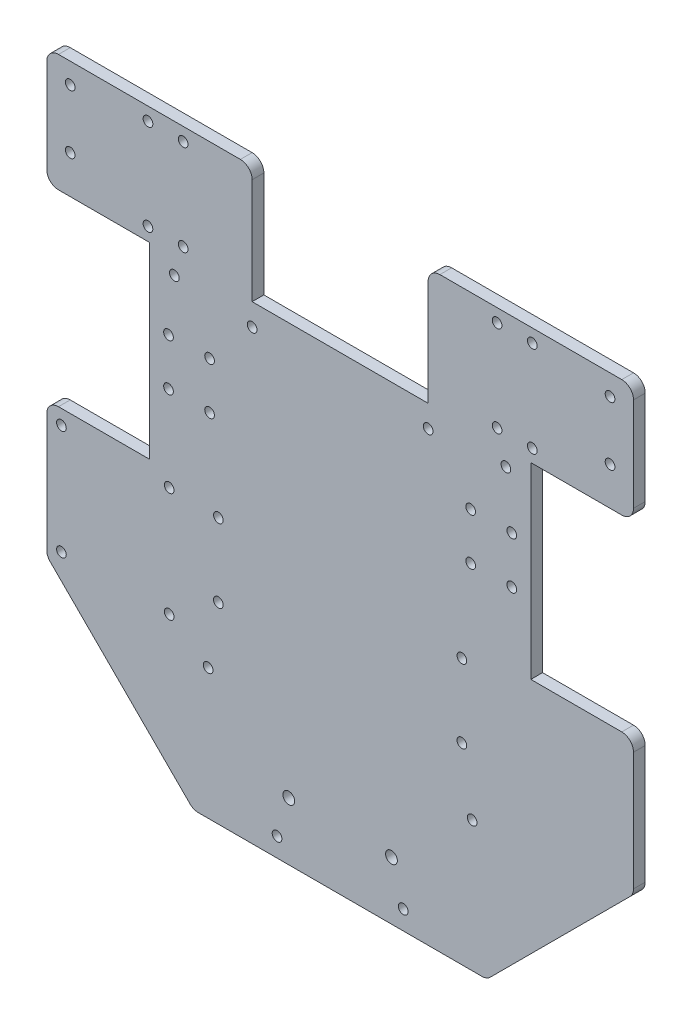
SolidWorks part; units mm, degrees
ref_plane "前视基准面" through (0, 0, 0) normal (0, 0, 1) x (1, 0, 0)
ref_plane "上视基准面" through (0, 0, 0) normal (0, 1, 0) x (1, 0, 0)
ref_plane "右视基准面" through (0, 0, 0) normal (1, 0, 0) x (0, 0, -1)
sketch "草图1" plane through (0, 0, 0) normal (0, 0, 1) x (1, 0, 0)
  line L0 (0, 0) -> (0, 207.9951) construction
  line L1 (-96, 200) -> (-30, 200)
  line L2 (-100, 196) -> (-100, 160)
  line L3 (-50, 0) -> (50, 0)
  line L4 (100, 196) -> (100, 160)
  line L5 (-100, 200) -> (74.6614, 24.6614) construction
  line L6 (-75.1068, 25.1068) -> (100, 200) construction
  line L7 (30, 200) -> (96, 200)
  line L8 (-30, 160) -> (30, 160)
  line L9 (-30, 160) -> (-30, 200)
  line L11 (30, 160) -> (30, 200)
  line L12 (-30, 160) -> (30, 200) construction
  line L13 (-30, 200) -> (30, 160) construction
  line L14 (100, 96) -> (65, 96)
  line L15 (-100, 160) -> (-65, 160)
  line L17 (-100, 96) -> (-65, 96)
  line L18 (-65, 160) -> (-65, 96)
  line L19 (65, 160) -> (65, 96)
  line L20 (100, 160) -> (65, 160)
  line L22 (-100, 96) -> (-100, 50)
  line L23 (100, 96) -> (100, 50)
  line L24 (-100, 50) -> (-50, 0)
  line L25 (100, 50) -> (50, 0)
  arc A0 (96, 200) -> (100, 196) centre (96, 196) cw
  arc A1 (-96, 200) -> (-100, 196) centre (-96, 196) ccw
  point P0 (-0.2545, 99.8678)
  point P7 (0, 180)
  dimension "D9" = 4
  dimension "D1" = 46
  dimension "D2" = 200
  dimension "D3" = 60
  dimension "D4" = 40
  dimension "D5" = 64
  dimension "D6" = 35
  dimension "D7" = 200
  dimension "D8" = 135
extrude "凸台-拉伸1" add sketch "草图1" along normal blind 4
sketch "草图4" plane through (0, 0, 0) normal (0, 0, -1) x (-1, 0, 0)
  line L1 (65, 160) -> (-65, 160) construction
  line L2 (65, 160) -> (65, 39) construction
  line L3 (65, 39) -> (-65, 39) construction
  line L4 (-65, 160) -> (-65, 39) construction
  line L5 (56.5, 154.5) -> (-56.5, 154.5) construction
  line L6 (56.5, 154.5) -> (56.5, 44.5) construction
  line L7 (56.5, 44.5) -> (-56.5, 44.5) construction
  line L8 (-56.5, 154.5) -> (-56.5, 44.5) construction
  line L10 (-30, 160) -> (30, 160) construction
  line L12 (65, 160) -> (65, 96) construction
  line L13 (-65, 96) -> (-65, 160) construction
  line L14 (0, 0) -> (0, 62.8556) construction
  circle A0 centre (56.5, 154.5) radius 1.65
  circle A1 centre (-56.5, 154.5) radius 1.65
  circle A4 centre (45, 44.5) radius 1.65
  circle A5 centre (-45, 44.5) radius 1.65
  dimension "D6" = 3.3
  dimension "D7" = 3.3
  dimension "D1" = 110
  dimension "D2" = 5.5
  dimension "D3" = 8.5
  dimension "D4" = 8.5
  dimension "D5" = 5.5
  dimension "D8" = 90
extrude "切除-拉伸5" cut sketch "草图4" against normal blind 10
sketch "草图5" plane through (0, 0, 0) normal (0, 0, -1) x (-1, 0, 0)
  line L0 (0, 0) -> (0, 78) construction
  line L1 (41.5, 90.5) -> (-41.5, 90.5) construction
  line L2 (41.5, 90.5) -> (41.5, 65.5) construction
  line L3 (41.5, 65.5) -> (-41.5, 65.5) construction
  line L4 (-41.5, 90.5) -> (-41.5, 65.5) construction
  line L5 (41.5, 90.5) -> (-41.5, 65.5) construction
  line L6 (41.5, 65.5) -> (-41.5, 90.5) construction
  line L7 (50, 0) -> (-50, 0) construction
  circle A0 centre (41.5, 90.5) radius 1.65
  circle A1 centre (-41.5, 90.5) radius 1.65
  circle A2 centre (41.5, 65.5) radius 1.65
  circle A3 centre (-41.5, 65.5) radius 1.65
  point P0 (0, 78)
  dimension "D4" = 3.3
  dimension "D1" = 65.5
  dimension "D2" = 83
  dimension "D3" = 25
extrude "切除-拉伸6" cut sketch "草图5" against normal blind 10
sketch "草图6" plane through (0, 0, 0) normal (0, 0, -1) x (-1, 0, 0)
  line L1 (58.26, 91) -> (95, 91) construction
  line L2 (58.26, 91) -> (58.26, 53.62) construction
  line L3 (58.26, 53.62) -> (95, 53.62) construction
  line L4 (95, 91) -> (95, 53.62) construction
  line L5 (65, 96) -> (100, 96) construction
  line L6 (100, 96) -> (100, 50) construction
  circle A1 centre (58.26, 91) radius 1.65
  circle A2 centre (95, 91) radius 1.65
  circle A3 centre (58.26, 53.62) radius 1.65
  circle A4 centre (95, 53.62) radius 1.65
  dimension "D3" = 5
  dimension "D5" = 3.3
  dimension "D1" = 37.38
  dimension "D2" = 36.74
  dimension "D4" = 5
extrude "切除-拉伸7" cut sketch "草图6" against normal blind 10
sketch "草图7" plane through (0, 0, 0) normal (0, 0, -1) x (-1, 0, 0)
  line L0 (0, 0) -> (0, 6.5) construction
  line L1 (50, 0) -> (-50, 0) construction
  line L2 (-21.5, 6.5) -> (21.5, 6.5) construction
  circle A0 centre (-21.5, 6.5) radius 1.65
  circle A1 centre (21.5, 6.5) radius 1.65
  dimension "D3" = 3.3
  dimension "D1" = 6.5
  dimension "D2" = 43
extrude "切除-拉伸8" cut sketch "草图7" against normal blind 10
sketch "草图8" plane through (0, 0, 0) normal (0, 0, -1) x (-1, 0, 0)
  line L0 (0, 0) -> (0, 19.75) construction
  line L1 (-17.5, 19.75) -> (17.5, 19.75) construction
  circle A0 centre (-17.5, 19.75) radius 2
  circle A1 centre (17.5, 19.75) radius 2
  dimension "D3" = 4
  dimension "D1" = 19.75
  dimension "D2" = 35
extrude "切除-拉伸9" cut sketch "草图8" against normal blind 10
sketch "草图9" plane through (0, 0, 0) normal (0, 0, -1) x (-1, 0, 0)
  line L0 (0, 160) -> (0, 152.5) construction
  line L1 (-30, 160) -> (30, 160) construction
  line L2 (-30, 152.5) -> (30, 152.5) construction
  circle A0 centre (-30, 152.5) radius 1.65
  circle A1 centre (30, 152.5) radius 1.65
  dimension "D2" = 3.3
  dimension "D1" = 60
  dimension "D3" = 7.5
extrude "切除-拉伸10" cut sketch "草图9" against normal blind 10
sketch "草图10" plane through (0, 0, 4) normal (0, 0, 1) x (1, 0, 0)
  line L1 (-100, 196) -> (-100, 160) construction
  line L2 (-100, 193) -> (-92, 193) construction
  line L3 (-92, 193) -> (-92, 173) construction
  line L4 (0, 160) -> (0, 0) construction
  line L5 (30, 160) -> (-30, 160) construction
  line L6 (-30, 200) -> (-96, 200) construction
  circle A0 centre (-92, 193) radius 1.65
  circle A1 centre (-92, 173) radius 1.65
  circle A2 centre (92, 173) radius 1.65
  circle A3 centre (92, 193) radius 1.65
  dimension "D3" = 3.3
  dimension "D5" = 3.3
  dimension "D2" = 8
  dimension "D4" = 20
  dimension "D6" = 7
extrude "切除-拉伸11" cut sketch "草图10" against normal blind 10
sketch "草图11" plane through (0, 0, 4) normal (0, 0, 1) x (1, 0, 0)
  line L0 (96, 200) -> (30, 200) construction
  line L1 (65.5, 164.5) -> (53.5, 164.5) construction
  line L2 (65.5, 164.5) -> (65.5, 195.5) construction
  line L3 (65.5, 195.5) -> (53.5, 195.5) construction
  line L4 (53.5, 164.5) -> (53.5, 195.5) construction
  line L5 (65.5, 164.5) -> (53.5, 195.5) construction
  line L6 (65.5, 195.5) -> (53.5, 164.5) construction
  line L7 (30, 200) -> (30, 160) construction
  line L8 (0, 0) -> (0, 212.3238) construction
  line L9 (-50, 0) -> (50, 0) construction
  line L10 (-65.5, 195.5) -> (-53.5, 164.5) construction
  line L11 (-65.5, 164.5) -> (-53.5, 195.5) construction
  line L12 (-53.5, 164.5) -> (-53.5, 195.5) construction
  line L13 (-65.5, 195.5) -> (-53.5, 195.5) construction
  line L15 (-65.5, 164.5) -> (-65.5, 195.5) construction
  line L16 (-65.5, 164.5) -> (-53.5, 164.5) construction
  circle A0 centre (65.5, 164.5) radius 1.65
  circle A1 centre (53.5, 164.5) radius 1.65
  circle A2 centre (53.5, 195.5) radius 1.65
  circle A3 centre (65.5, 195.5) radius 1.65
  circle A8 centre (-65.5, 195.5) radius 1.65
  circle A9 centre (-53.5, 195.5) radius 1.65
  circle A10 centre (-53.5, 164.5) radius 1.65
  circle A11 centre (-65.5, 164.5) radius 1.65
  dimension "D1" = 3.3
  dimension "D2" = 4.5
  dimension "D3" = 31
  dimension "D4" = 12
  dimension "D5" = 23.5
extrude "切除-拉伸12" cut sketch "草图11" against normal blind 10
sketch "草图12" plane through (0, 0, 4) normal (0, 0, 1) x (1, 0, 0)
  line L0 (100, 96) -> (65, 96) construction
  line L1 (58.5, 136) -> (44.5, 136) construction
  line L2 (58.5, 136) -> (58.5, 120) construction
  line L3 (58.5, 120) -> (44.5, 120) construction
  line L4 (44.5, 136) -> (44.5, 120) construction
  line L5 (58.5, 136) -> (44.5, 120) construction
  line L6 (58.5, 120) -> (44.5, 136) construction
  line L8 (100, 160) -> (100, 196) construction
  line L9 (0, 0) -> (0, 113.8804) construction
  line L10 (-50, 0) -> (50, 0) construction
  line L11 (-58.5, 120) -> (-44.5, 136) construction
  line L12 (-58.5, 136) -> (-44.5, 120) construction
  line L13 (-44.5, 136) -> (-44.5, 120) construction
  line L14 (-58.5, 120) -> (-44.5, 120) construction
  line L15 (-58.5, 136) -> (-58.5, 120) construction
  line L16 (-58.5, 136) -> (-44.5, 136) construction
  circle A0 centre (58.5, 120) radius 1.65
  circle A1 centre (44.5, 120) radius 1.65
  circle A2 centre (44.5, 136) radius 1.65
  circle A3 centre (58.5, 136) radius 1.65
  circle A4 centre (-58.5, 136) radius 1.65
  circle A5 centre (-44.5, 136) radius 1.65
  circle A6 centre (-44.5, 120) radius 1.65
  circle A7 centre (-58.5, 120) radius 1.65
  point P0 (51.5, 128)
  point P25 (-51.5, 128)
  dimension "D3" = 3.3
  dimension "D1" = 14
  dimension "D2" = 16
  dimension "D4" = 32
  dimension "D5" = 41.5
extrude "切除-拉伸13" cut sketch "草图12" against normal blind 10
fillet "圆角1" radius 4 8 edges at (100, 96, 2) (100, 160, 2) (100, 50, 2) (50, 0, 2) (-50, 0, 2) (-100, 50, 2) (-100, 96, 2) (-100, 160, 2)
fillet "圆角2" radius 4 2 edges at (30, 200, 2) (-30, 200, 2)
